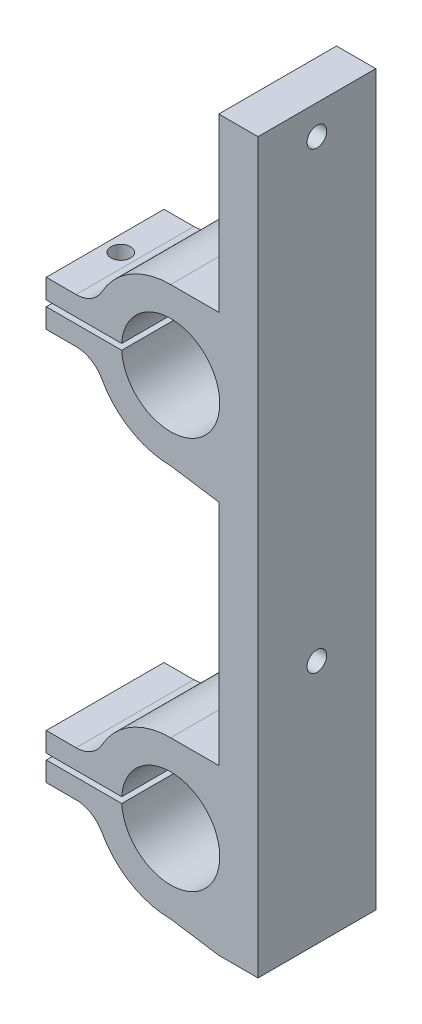
SolidWorks part; units mm, degrees
ref_plane "前视基准面" through (0, 0, 0) normal (0, 0, 1) x (1, 0, 0)
ref_plane "上视基准面" through (0, 0, 0) normal (0, 1, 0) x (1, 0, 0)
ref_plane "右视基准面" through (0, 0, 0) normal (1, 0, 0) x (0, 0, -1)
sketch "草图1" plane through (0, 0, 0) normal (0, 0, 1) x (1, 0, 0)
  line L0 (0, 8) -> (4.9, 8)
  line L1 (0, -8) -> (4.9, -8.754)
  line L2 (8.9, 25.5) -> (8.9, -48.754)
  line L3 (4.9, 25.5) -> (4.9, 8)
  line L4 (4.9, 25.5) -> (8.9, 25.5)
  line L5 (8.9, 25.5) -> (8.9, -31) construction
  line L6 (4.9, -8.754) -> (4.9, -31)
  line L7 (-4.991, -40.3) -> (-12.6812, -40.3)
  line L8 (4.9, 25.5) -> (4.9, -31) construction
  line L9 (-12.6812, -37.7) -> (-12.6812, -39.7)
  line L10 (-9.639, -42.3) -> (-12.6812, -42.3)
  line L11 (-4.991, -39.7) -> (-12.6812, -39.7)
  line L12 (-12.6812, 2.3) -> (-12.6812, 0.3)
  line L13 (-12.6812, -0.3) -> (-12.6812, -2.3)
  line L14 (-9.639, 2.3) -> (-12.6812, 2.3)
  line L15 (-4.991, 0.3) -> (-12.6812, 0.3)
  line L16 (-9.639, -37.7) -> (-12.6812, -37.7)
  line L17 (-4.991, -0.3) -> (-12.6812, -0.3)
  line L18 (-12.6812, -40.3) -> (-12.6812, -42.3)
  line L19 (-9.639, -2.3) -> (-12.6812, -2.3)
  line L20 (0, -32) -> (4.9, -32)
  line L21 (0, -48) -> (4.9, -48.754)
  line L22 (4.9, -48.754) -> (8.9, -48.754)
  line L23 (4.9, -31) -> (4.9, -32)
  arc A0 (-4.991, -0.3) -> (-4.991, 0.3) centre (0, 0) ccw
  arc A1 (0, 8) -> (-7.0102, 3.8545) centre (0, 0) ccw
  arc A2 (-7.0102, -3.8545) -> (0, -8) centre (0, 0) ccw
  circle A3 centre (0, 0) radius 8 construction
  circle A4 centre (0, 0) radius 5 construction
  arc A5 (-9.639, -2.3) -> (-7.0102, -3.8545) centre (-9.639, -5.3) cw
  arc A6 (-9.639, 2.3) -> (-7.0102, 3.8545) centre (-9.639, 5.3) ccw
  arc A7 (-4.991, -40.3) -> (-4.991, -39.7) centre (0, -40) ccw
  arc A8 (0, -32) -> (-7.0102, -36.1455) centre (0, -40) ccw
  arc A9 (-7.0102, -43.8545) -> (0, -48) centre (0, -40) ccw
  arc A10 (-9.639, -37.7) -> (-7.0102, -36.1455) centre (-9.639, -34.7) ccw
  arc A11 (-9.639, -42.3) -> (-7.0102, -43.8545) centre (-9.639, -45.3) cw
  point P8 (0, 0.3)
  point P13 (8, 0)
  point P15 (0, 2.3)
  point P17 (0, -0.3)
  point P22 (0, -2.3)
  point P25 (4.7815, 1.4619)
  point P28 (-7.6622, -2.3)
  dimension "D1" = 10
  dimension "D3" = 3
  dimension "D8" = 40
  dimension "D4" = 4.9
  dimension "D5" = 25.5
  dimension "D2" = 3
  dimension "D7" = 4
extrude "凸台-拉伸1" add sketch "草图1" along normal blind 12
sketch "草图2" plane through (4.9, 0, 0) normal (-1, 0, 0) x (0, 0, 1)
  line L0 (12, 25.5) -> (0, 25.5) construction
  line L2 (12, -8.754) -> (12, -32) construction
  line L3 (12, 25.5) -> (12, 8) construction
  circle A0 centre (6, 22.5) radius 1
  circle A1 centre (6, -23.78) radius 1
  dimension "D1" = 2
  dimension "D2" = 2
  dimension "D3" = 3
  dimension "D4" = 46.28
  dimension "D5" = 6
  dimension "D6" = 6
extrude "切除-拉伸1" cut sketch "草图2" against normal blind 4
sketch "草图3" plane through (0, 2.3, 0) normal (0, 1, 0) x (1, 0, 0)
  line L0 (-9.639, 0) -> (-12.6812, 0) construction
  line L1 (-12.6812, -12) -> (-12.6812, 0) construction
  circle A0 centre (-11.0812, -6) radius 1
  dimension "D1" = 2
  dimension "D2" = 6
  dimension "D3" = 1.6
extrude "切除-拉伸2" cut sketch "草图3" against normal blind 10
